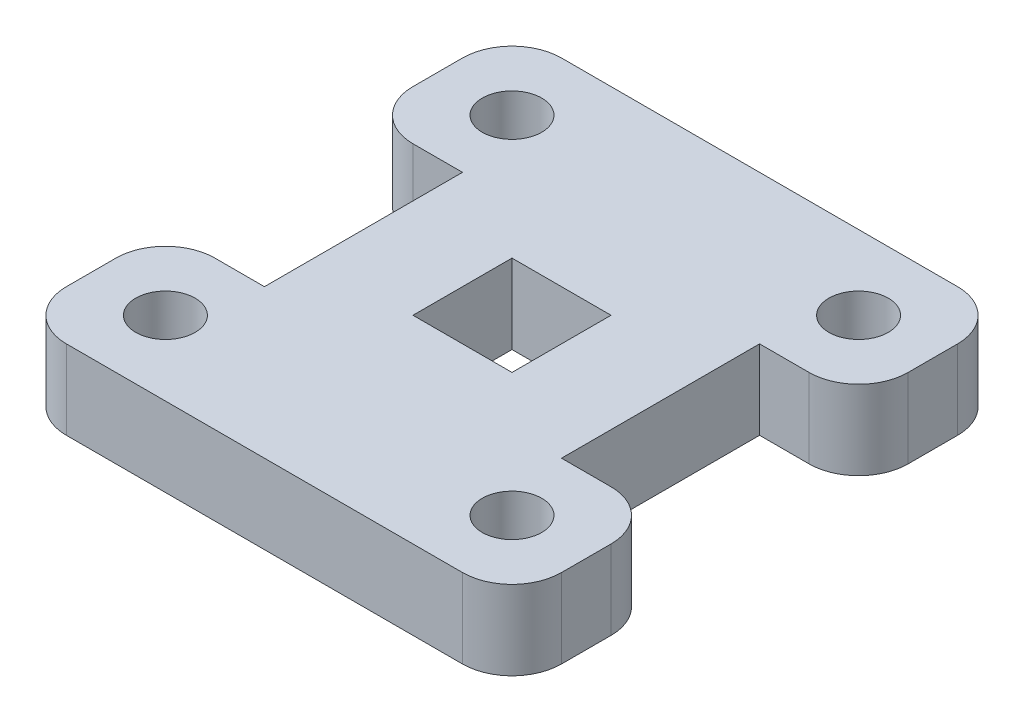
SolidWorks part; units mm, degrees
ref_plane "Front Plane" through (0, 0, 0) normal (0, 0, 1) x (1, 0, 0)
ref_plane "Top Plane" through (0, 0, 0) normal (0, 1, 0) x (1, 0, 0)
ref_plane "Right Plane" through (0, 0, 0) normal (1, 0, 0) x (0, 0, -1)
sketch "Sketch1" plane through (0, 0, 0) normal (0, 1, 0) x (1, 0, 0)
  line L0 (-30, 20) -> (-30, -20)
  line L1 (-40, -50) -> (40, -50)
  line L2 (-50, -40) -> (-50, -30)
  line L3 (-40, 50) -> (40, 50)
  line L4 (50, -40) -> (50, -30)
  line L5 (30, 20) -> (30, -20)
  line L6 (-40, 20) -> (-30, 20)
  line L7 (-40, -20) -> (-30, -20)
  line L8 (-50, 30) -> (-50, 40)
  line L9 (50, 30) -> (50, 40)
  line L10 (30, 20) -> (40, 20)
  line L11 (30, -20) -> (40, -20)
  line L12 (0, 50) -> (0, -52.2465) construction
  line L17 (-10, -10) -> (10, -10)
  line L18 (-10, -10) -> (-10, 10)
  line L19 (-10, 10) -> (10, 10)
  line L20 (10, -10) -> (10, 10)
  line L21 (-10, -10) -> (10, 10) construction
  line L22 (-10, 10) -> (10, -10) construction
  line L23 (-30, 0) -> (30, 0) construction
  arc A0 (40, -20) -> (50, -30) centre (40, -30) cw
  arc A1 (40, -50) -> (50, -40) centre (40, -40) ccw
  arc A2 (-40, -50) -> (-50, -40) centre (-40, -40) cw
  arc A3 (-40, -20) -> (-50, -30) centre (-40, -30) ccw
  arc A4 (-40, 20) -> (-50, 30) centre (-40, 30) cw
  arc A5 (40, 20) -> (50, 30) centre (40, 30) ccw
  arc A6 (40, 50) -> (50, 40) centre (40, 40) cw
  arc A7 (-50, 40) -> (-40, 50) centre (-40, 40) cw
  circle A8 centre (-35, 35) radius 6
  circle A9 centre (35, 35) radius 6
  circle A10 centre (35, -35) radius 6
  circle A11 centre (-35, -35) radius 6
  point P4 (0, 0)
  point P12 (0, 50)
  point P23 (50, -50)
  point P30 (-50, 20)
  point P33 (50, 20)
  point P36 (50, 50)
  point P39 (-50, 50)
  point P42 (-50, 35)
  dimension "D11" = 10
  dimension "D12" = 12
  dimension "D13" = 15
  dimension "D14" = 15
  dimension "D1" = 100
  dimension "D2" = 100
  dimension "D3" = 20
  dimension "D4" = 20
  dimension "D5" = 30
  dimension "D6" = 30
  dimension "D7" = 50
  dimension "D8" = 50
  dimension "D9" = 20
  dimension "D10" = 20
extrude "Boss-Extrude1" add sketch "Sketch1" along normal blind 16
